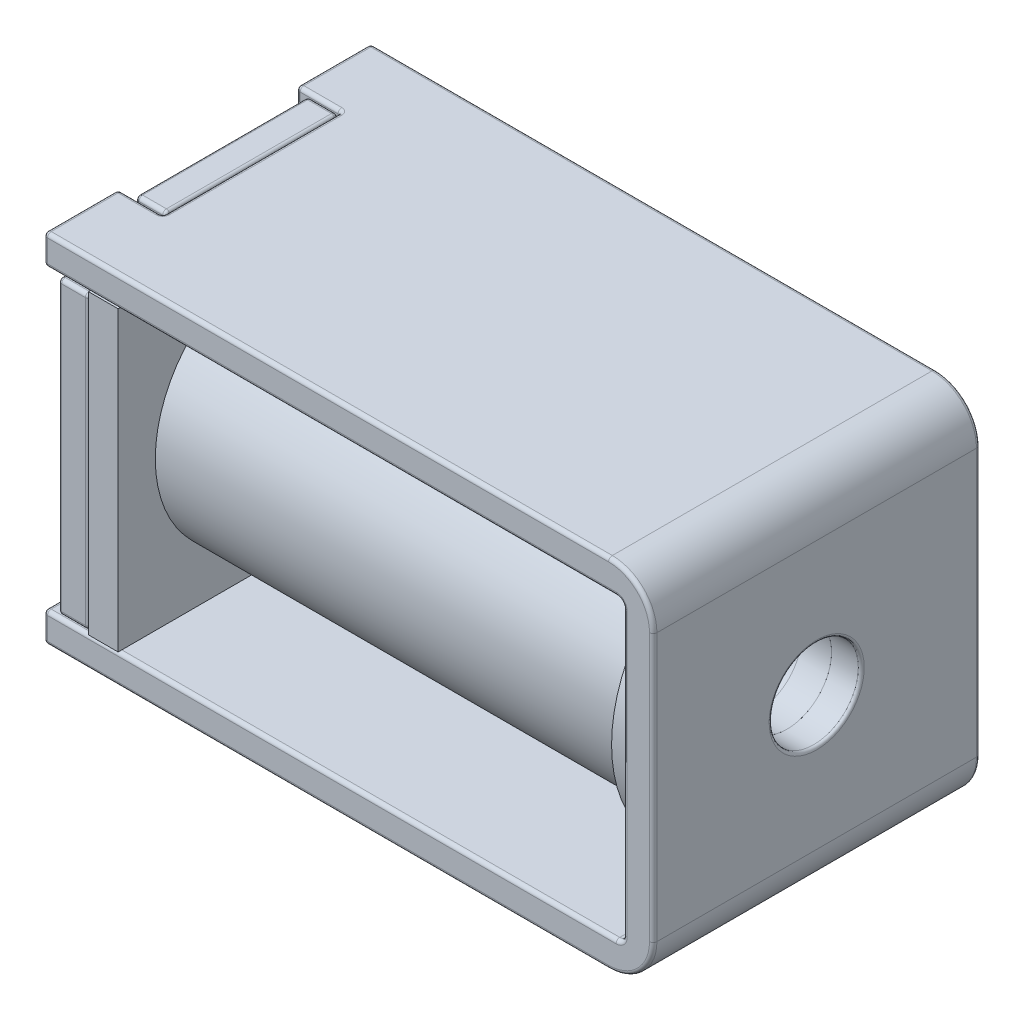
SolidWorks part; units mm, degrees
ref_plane "Front Plane" through (0, 0, 0) normal (0, 0, 1) x (1, 0, 0)
ref_plane "Top Plane" through (0, 0, 0) normal (0, 1, 0) x (1, 0, 0)
ref_plane "Right Plane" through (0, 0, 0) normal (1, 0, 0) x (0, 0, -1)
sketch "Sketch1" plane through (0, 0, 0) normal (0, 0, 1) x (1, 0, 0)
  line L0 (0, 0) -> (20.5, 0)
  line L1 (20.5, 0) -> (20.5, -12)
  line L2 (20.5, -12) -> (0, -12)
  line L3 (0, 0) -> (0, -1)
  line L4 (0, -1) -> (19.5, -1)
  line L5 (19.5, -1) -> (19.5, -11)
  line L6 (19.5, -11) -> (0, -11)
  line L7 (0, -11) -> (0, -12)
  dimension "D1" = 20.5
  dimension "D2" = 12
  dimension "D3" = 1
  dimension "D4" = 1
extrude "Boss-Extrude1" add sketch "Sketch1" along normal blind 11
sketch "Sketch2" plane through (0, 0, 0) normal (-1, 0, 0) x (0, 0, 1)
  line L0 (5.5, -1000) -> (5.5, 49000) construction
  line L1 (8.5, 0) -> (8.5, -1)
  line L2 (-994.5, -6) -> (49005.5, -6) construction
  line L3 (8.5, 0) -> (2.5, 0)
  line L4 (2.5, 0) -> (2.5, -1)
  line L5 (11, -1) -> (0, -1) construction
  line L6 (0, 0) -> (0, -1) construction
  line L7 (2.5, -1) -> (8.5, -1)
  line L9 (11, 0) -> (0, 0) construction
  line L11 (2.5, -11) -> (8.5, -11)
  line L12 (2.5, -12) -> (2.5, -11)
  line L13 (8.5, -12) -> (2.5, -12)
  line L14 (8.5, -12) -> (8.5, -11)
  point P3 (5.5, -1)
  point P8 (5.5, 0)
  point P24 (5.5, -12)
  point P25 (5.5, -11)
  dimension "D1" = 3
  dimension "D2" = 2.5
  dimension "D3" = 1
  dimension "D4" = 6
extrude "Cut-Extrude1" cut sketch "Sketch2" against normal blind 1.5
sketch "Sketch3" plane through (1.5, 0, 0) normal (-1, 0, 0) x (0, 0, 1)
  line L0 (2.6, 0) -> (2.6, -1.1)
  line L1 (8.5, 0) -> (2.5, 0) construction
  line L2 (2.6, -1.1) -> (0, -1.1)
  line L3 (0, -1) -> (0, -11) construction
  line L4 (0, -1.1) -> (0, -10.9)
  line L5 (-1000, -6) -> (49000, -6) construction
  line L6 (11, -1) -> (0, -1) construction
  line L7 (2.5, 0) -> (2.5, -1) construction
  line L8 (2.6, 0) -> (8.4, 0)
  line L9 (8.4, 0) -> (8.4, -1.1)
  line L10 (8.4, -1.1) -> (11, -1.1)
  line L11 (11, -1) -> (11, -11) construction
  line L12 (11, -1.1) -> (11, -10.9)
  line L13 (8.5, -1) -> (8.5, 0) construction
  line L14 (11, -1) -> (8.5, -1) construction
  line L15 (8.4, -10.9) -> (11, -10.9)
  line L16 (8.4, -12) -> (8.4, -10.9)
  line L17 (2.6, -12) -> (8.4, -12)
  line L18 (2.6, -10.9) -> (0, -10.9)
  line L19 (2.6, -12) -> (2.6, -10.9)
  point P25 (11, -6)
  point P29 (0, -6)
  dimension "D1" = 0.1
  dimension "D2" = 0.1
  dimension "D3" = 0.1
  dimension "D4" = 0.1
extrude "Boss-Extrude2" add sketch "Sketch3" along normal blind 1 separate body
fillet "Fillet1" radius 0.125 8 edges at (1, -1.1, 11) (1, 0, 8.4) (1, 0, 2.6) (1, -1.1, 0) (1, -10.9, 0) (1, -12, 2.6) (1, -12, 8.4) (1, -10.9, 11)
fillet "Fillet2" radius 0.1 20 edges at (0.5, -10.8634, 10.9634) (0.5, -10.9, 9.6375) (0.5, -11.3875, 8.4) (0.5, -11.9634, 8.3634) (0.5, -12, 5.5) (0.5, -11.9634, 2.6366) (0.5, -11.3875, 2.6) (0.5, -10.9, 1.3625) (0.5, -10.8634, 0.0366) (0.5, -6, 0) (0.5, -1.1366, 0.0366) (0.5, -1.1, 1.3625) (0.5, -0.6125, 2.6) (0.5, -0.0366, 2.6366) (0.5, 0, 5.5) (0.5, -0.0366, 8.3634) (0.5, -0.6125, 8.4) (0.5, -1.1, 9.6375) (0.5, -1.1366, 10.9634) (0.5, -6, 11)
fillet "Fillet3" radius 0.1 20 edges at (1.5, -0.6125, 8.4) (1.5, -0.0366, 8.3634) (1.5, 0, 5.5) (1.5, -0.0366, 2.6366) (1.5, -0.6125, 2.6) (1.5, -1.1, 1.3625) (1.5, -1.1366, 0.0366) (1.5, -6, 0) (1.5, -10.8634, 0.0366) (1.5, -10.9, 1.3625) (1.5, -11.3875, 2.6) (1.5, -11.9634, 2.6366) (1.5, -12, 5.5) (1.5, -11.9634, 8.3634) (1.5, -11.3875, 8.4) (1.5, -10.9, 9.6375) (1.5, -10.8634, 10.9634) (1.5, -6, 11) (1.5, -1.1366, 10.9634) (1.5, -1.1, 9.6375)
fillet "Fillet4" radius 0.1 12 edges at (0.5293, -10.8707, 8.3707) (1.4707, -10.8707, 8.3707) (0.5293, -10.8707, 2.6293) (1.4707, -10.8707, 2.6293) (0.5293, -1.1293, 2.6293) (1.4707, -1.1293, 2.6293) (0.5293, -1.1293, 8.3707) (1.4707, -1.1293, 8.3707) (1, -10.9, 8.4) (1, -10.9, 2.6) (1, -1.1, 2.6) (1, -1.1, 8.4)
fillet "Fillet6" radius 0.1 4 edges at (1.5, -0.5, 8.5) (1.5, -0.5, 2.5) (1.5, -11.5, 2.5) (1.5, -11.5, 8.5)
fillet "Fillet8" radius 1.5 2 edges at (20.5, -12, 5.5) (20.5, 0, 5.5)
fillet "Fillet9" radius 0.25 2 edges at (19.5, -11, 5.5) (19.5, -1, 5.5)
fillet "Fillet10" radius 0.125 56 edges at (20.0607, -0.4393, 0) (19.4268, -1.0732, 0) (19.4268, -10.9268, 0) (20.0607, -11.5607, 0) (19.4268, -10.9268, 11) (19.4268, -1.0732, 11) (20.0607, -0.4393, 11) (20.0607, -11.5607, 11) (20.5, -6, 0) (20.5, -6, 11) (0.7, -12, 2.5) (1.4707, -12, 2.5293) (1.5, -12, 5.5) (1.4707, -12, 8.4707) (0.7, -12, 8.5) (9.5, -12, 11) (9.5, -12, 0) (0.7, -1, 2.5) (1.4707, -1, 2.5293) (1.5, -1, 5.5) (1.4707, -1, 8.4707) (0.7, -1, 8.5) (9.625, -1, 11) (9.625, -1, 0) (0.7, -11, 8.5) (1.4707, -11, 8.4707) (1.5, -11, 5.5) (1.4707, -11, 2.5293) (0.7, -11, 2.5) (9.625, -11, 0) (9.625, -11, 11) (0, -11.5, 0) (0, -11, 1.25) (0, -11.5, 2.5) (0, -12, 1.25) (0, -11.5, 11) (0, -12, 9.75) (0, -11.5, 8.5) (0, -11, 9.75) (0, -0.5, 11) (0, -1, 9.75) (0, -0.5, 8.5) (0, -0.5, 0) (0, -0.5, 2.5) (0, -1, 1.25) (19.5, -6, 11) (19.5, -6, 0) (0, 0, 9.75) (0.7, 0, 8.5) (1.4707, 0, 8.4707) (1.5, 0, 5.5) (1.4707, 0, 2.5293) (0.7, 0, 2.5) (0, 0, 1.25) (9.5, 0, 0) (9.5, 0, 11)
sketch "Sketch4" plane through (1.5, 0, 0) normal (1, 0, 0) x (0, 0, -1)
  line L0 (-1010.9, -6) -> (48989.1, -6) construction
  line L1 (-10.9, -1.225) -> (-10.9, -10.775) construction
  line L2 (-5.5, -1000.1) -> (-5.5, 48999.9) construction
  line L3 (-2.725, -0.1) -> (-8.275, -0.1) construction
  line L5 (-11, -11) -> (0, -11)
  line L6 (-11, -11) -> (-11, -1)
  line L7 (-11, -1) -> (0, -1)
  line L8 (0, -11) -> (0, -1)
  line L9 (-11, -11) -> (0, -1) construction
  line L10 (-11, -1) -> (0, -11) construction
  point P5 (-10.9, -6)
  point P6 (-5.5, -6)
  point P10 (-5.5, -0.1)
  dimension "D1" = 10
  dimension "D2" = 11
extrude "Boss-Extrude3" add sketch "Sketch4" along normal blind 1 separate body
sketch "Sketch6" plane through (0.5, 0, 0) normal (-1, 0, 0) x (0, 0, 1)
  line L0 (-999.9, -6) -> (49000.1, -6) construction
  line L1 (0.1, -1.225) -> (0.1, -10.775) construction
  line L2 (5.5, -1000.1) -> (5.5, 48999.9) construction
  line L3 (8.275, -0.1) -> (2.725, -0.1) construction
  circle A0 centre (5.5, -6) radius 2.25
  point P5 (0.1, -6)
  point P10 (5.5, -0.1)
extrude "Cut-Extrude3" cut sketch "Sketch6" against normal blind 2
sketch "Sketch7" plane through (19.5, 0, 0) normal (-1, 0, 0) x (0, 0, 1)
  line L0 (0, -10.775) -> (0, -1.225) construction
  line L1 (2.725, 0) -> (8.275, 0) construction
  circle A0 centre (5.5, -6) radius 4.9
  dimension "D1" = 9.8
  dimension "D2" = 5.5
  dimension "D3" = 6
extrude "Boss-Extrude4" add sketch "Sketch7" along normal blind 1 separate body
sketch "Sketch8" plane through (18.5, 0, 0) normal (-1, 0, 0) x (0, 0, 1)
  line L1 (0, -10.75) -> (0, -1.25) construction
  line L2 (10.875, 0) -> (0.125, 0) construction
  circle A0 centre (5.5, -6) radius 4.25
  dimension "D1" = 8.5
  dimension "D2" = 5.5
  dimension "D3" = 6
extrude "Boss-Extrude5" add sketch "Sketch8" along normal up to surface (16 mm away) separate body
sketch "Sketch9" plane through (20.5, 0, 0) normal (1, 0, 0) x (0, 0, -1)
  line L0 (-5.5, -1001.5) -> (-5.5, 48998.5) construction
  line L1 (-0.125, -1.5) -> (-10.875, -1.5) construction
  line L2 (-1010.875, -6) -> (48989.125, -6) construction
  line L3 (-10.875, -1.5) -> (-10.875, -10.5) construction
  circle A0 centre (-5.5, -6) radius 1.5
  point P5 (-5.5, -1.5)
  point P10 (-10.875, -6)
extrude "Cut-Extrude4" cut sketch "Sketch9" against normal through all
fillet "Fillet14" radius 0.1 1 edges at (20.5, -4.5, 5.5)
fillet "Fillet15" radius 0.1 1 edges at (0.5, -8.25, 5.5)
